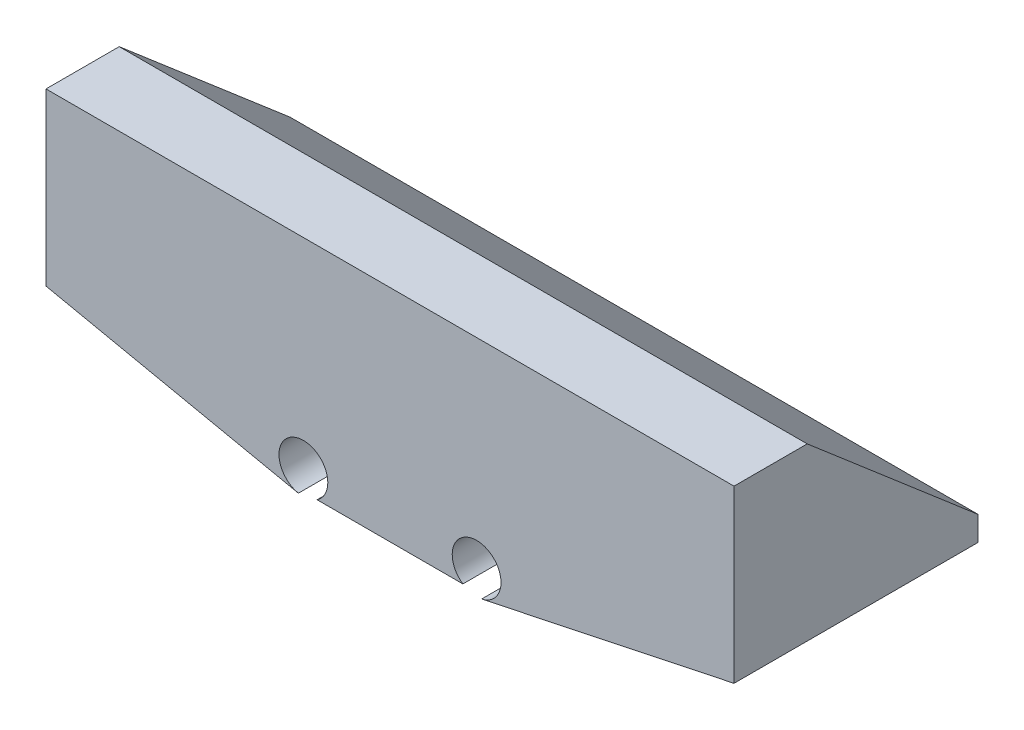
SolidWorks part; units mm, degrees
ref_plane "Front Plane" through (0, 0, 0) normal (0, 0, 1) x (1, 0, 0)
ref_plane "Top Plane" through (0, 0, 0) normal (0, 1, 0) x (1, 0, 0)
ref_plane "Right Plane" through (0, 0, 0) normal (1, 0, 0) x (0, 0, -1)
ref_plane "Plane1" through (0, 0, 17) normal (0, 0, 1) x (1, 0, 0)
sketch "Sketch2" plane through (0, 0, 17) normal (0, 0, 1) x (1, 0, 0)
  line L0 (11.6724, 96.3914) -> (-11.7805, 96.3914) construction
  line L1 (-17.8013, 90.3914) -> (-17.8013, 109.6026) construction
  line L2 (70.4445, 96.3914) -> (18.7236, 85.4987)
  line L3 (-0.0541, 90.3914) -> (-0.0541, 109.6026) construction
  line L4 (-0.0541, 96.3914) -> (-14.9939, 86.2539) construction
  line L5 (-70.5526, 96.3914) -> (-18.8317, 85.4987)
  line L6 (-0.0541, 96.3914) -> (14.8857, 86.2539) construction
  line L7 (-70.5526, 19.3914) -> (-70.5526, -73.6086) construction
  line L8 (-70.5526, 101.3914) -> (70.4445, 101.3914)
  line L9 (-70.5526, 101.3914) -> (-70.5526, 96.3914)
  line L10 (-70.5526, 96.3914) -> (70.4445, 96.3914) construction
  line L11 (70.4445, 101.3914) -> (70.4445, 96.3914)
  line L12 (70.4445, -73.6086) -> (70.4445, 19.3914) construction
  line L13 (-14.9939, 86.2539) -> (14.8857, 86.2539)
  circle A4 centre (-17.8013, 90.3914) radius 5
  circle A5 centre (17.6932, 90.3914) radius 5
  arc A6 (18.7236, 85.4987) -> (14.8857, 86.2539) centre (17.6932, 90.3914) ccw
  arc A7 (-14.9939, 86.2539) -> (-18.8317, 85.4987) centre (-17.8013, 90.3914) ccw
  dimension "D2" = 0
  dimension "D3" = 0
  dimension "D10" = 5
extrude "Boss-Extrude1" add sketch "Sketch2" against normal blind 50
sketch "Sketch7" plane through (-70.5526, 0, 0) normal (-1, 0, 0) x (0, 0, 1)
  line L0 (17, 131.3914) -> (2, 131.3914)
  line L1 (2, 131.3914) -> (-33, 101.3914)
  line L2 (17, 131.3914) -> (17, 101.3914)
  line L3 (-33, 101.3914) -> (17, 101.3914)
  dimension "D1" = 30
  dimension "D2" = 15
extrude "Boss-Extrude2" add sketch "Sketch7" against normal up to surface (140.9971 mm away) up to face at (70.4445, 98.8914, -8)
